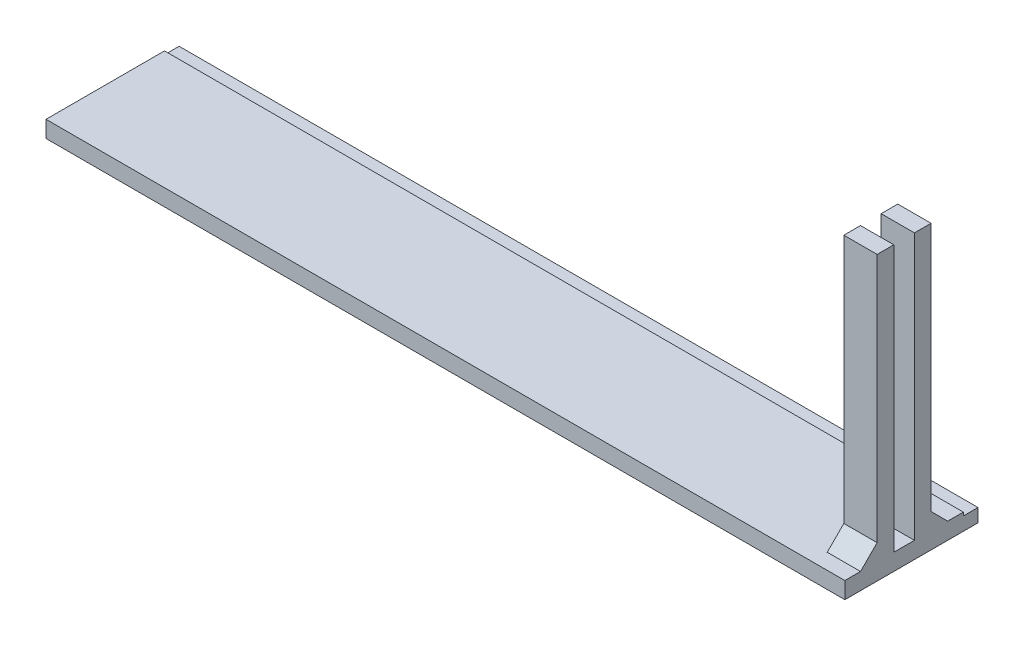
SolidWorks part; units mm, degrees
ref_plane "Front Plane" through (0, 0, 0) normal (0, 0, 1) x (1, 0, 0)
ref_plane "Top Plane" through (0, 0, 0) normal (0, 1, 0) x (1, 0, 0)
ref_plane "Right Plane" through (0, 0, 0) normal (1, 0, 0) x (0, 0, -1)
sketch "Sketch1" plane through (0, 0, 0) normal (0, 1, 0) x (1, 0, 0)
  line L1 (0, 0) -> (152.4, 0)
  line L2 (0, 0) -> (0, 25.4)
  line L3 (0, 25.4) -> (152.4, 25.4)
  line L4 (152.4, 0) -> (152.4, 25.4)
  dimension "D1" = 152.4
  dimension "D2" = 25.4
extrude "Boss-Extrude1" add sketch "Sketch1" along normal blind 3.175
sketch "Sketch2" plane through (0, 3.175, 0) normal (0, 1, 0) x (1, 0, 0)
  line L0 (152.4, 0) -> (152.4, 25.4) construction
  line L1 (0, 25.4) -> (152.4, 25.4)
  line L2 (0, 25.4) -> (0, 22.606)
  line L3 (0, 22.606) -> (152.4, 22.606)
  line L4 (152.4, 25.4) -> (152.4, 22.606)
  dimension "D1" = 2.794
extrude "Cut-Extrude1" cut sketch "Sketch2" against normal blind 0.635
sketch "Sketch4" plane through (152.4, 0, 0) normal (1, 0, 0) x (0, 0, -1)
  line L0 (0, 3.175) -> (22.606, 3.175) construction
  line L5 (6.1595, 3.175) -> (9.3345, 3.175)
  line L6 (6.1595, 3.175) -> (6.1595, 53.975)
  line L7 (6.1595, 53.975) -> (9.3345, 53.975)
  line L8 (9.3345, 3.175) -> (9.3345, 53.975)
  line L9 (11.303, 3.175) -> (11.303, 29.9743) construction
  line L10 (13.2715, 3.175) -> (16.4465, 3.175)
  line L11 (13.2715, 3.175) -> (13.2715, 53.975)
  line L12 (13.2715, 53.975) -> (16.4465, 53.975)
  line L13 (16.4465, 3.175) -> (16.4465, 53.975)
  dimension "D1" = 3.175
  dimension "D2" = 3.937
  dimension "D3" = 50.8
extrude "Boss-Extrude2" add sketch "Sketch4" against normal blind 6.35
ref_plane "Plane2" through (76.2, 0, 0) normal (-1, 0, 0) x (0, 0, 1)
chamfer "Chamfer2" distance 3.175 angle 45 2 edges at (149.225, 3.175, -16.4465) (149.225, 3.175, -6.1595)
